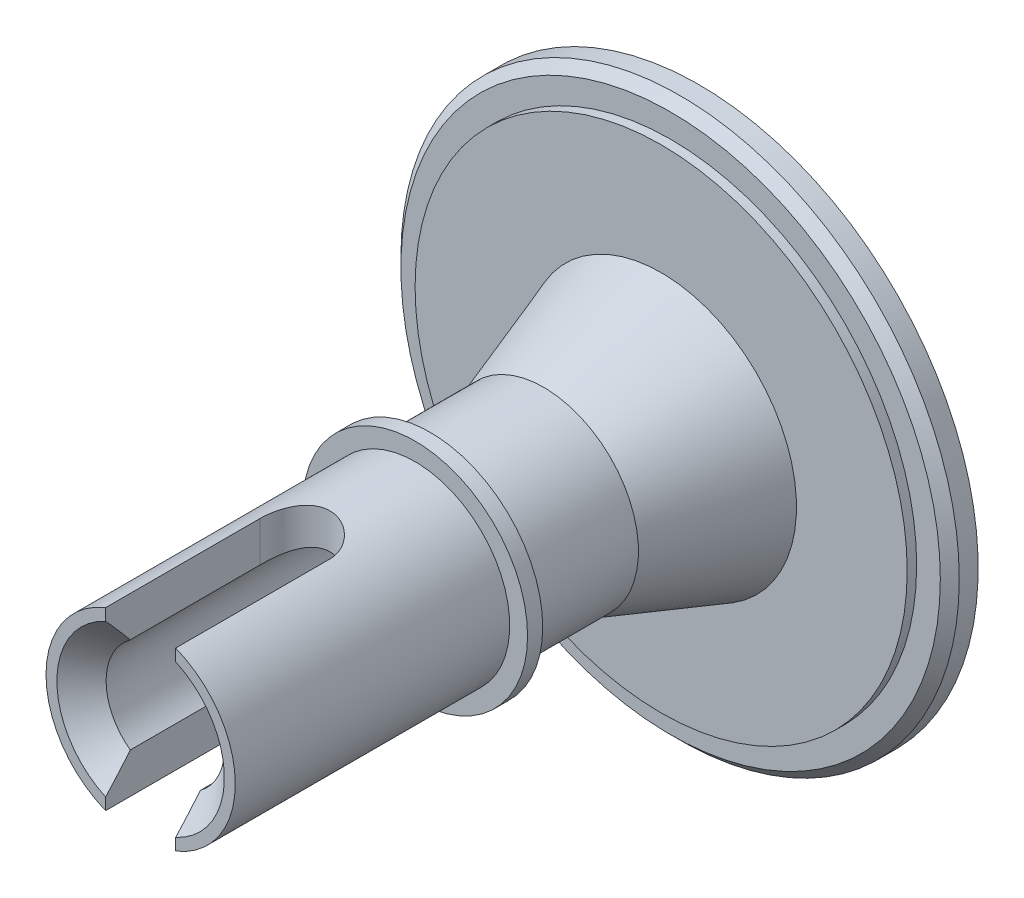
SolidWorks part; units mm, degrees
material "PVC hart"
ref_plane "Ebene vorne" through (0, 0, 0) normal (0, 0, 1) x (1, 0, 0)
ref_plane "Ebene oben" through (0, 0, 0) normal (0, 1, 0) x (1, 0, 0)
ref_plane "Ebene rechts" through (0, 0, 0) normal (1, 0, 0) x (0, 0, -1)
sketch "Skizze2" plane through (0, 0, 0) normal (1, 0, 0) x (0, 0, -1)
  line L0 (10.6064, 0) -> (-45.5592, 0) construction
  line L1 (0, 14.75) -> (-1.5, 14.75)
  line L2 (-1.5, 14.75) -> (-1.5, 13)
  line L3 (-1.5, 13) -> (-2, 13)
  line L4 (-2, 13) -> (-2, 7.15)
  line L5 (0.5, 7.5) -> (0, 7.5)
  line L6 (0.5, 7.5) -> (0.5, 9.5)
  line L7 (0.5, 9.5) -> (0, 9.5)
  line L8 (0, 9.5) -> (0, 12.65)
  line L9 (0, 7.5) -> (0, 3.9)
  line L10 (0, 3.9) -> (-2, 3.9)
  line L11 (-2, 3.9) -> (-2, 1.45)
  line L12 (-2, 1.45) -> (-4.5, 1.45)
  line L13 (-4.5, 1.45) -> (-4.5, 3.125)
  line L14 (-4.5, 3.125) -> (-29.5, 3.125)
  line L15 (-29.5, 3.125) -> (-29.5, 5)
  line L16 (-29.5, 5) -> (-15, 5)
  line L17 (0, 3.9) -> (0, 0) construction
  line L18 (0, 14.15) -> (-0.8, 14.15)
  line L19 (-0.8, 14.15) -> (-0.8, 12.65)
  line L20 (-0.8, 12.65) -> (0, 12.65)
  line L21 (0, 14.15) -> (0, 14.75)
  line L22 (-15, 5) -> (-15, 5.9425)
  line L23 (-15, 5.9425) -> (-14.2, 5.9425)
  line L24 (-14.2, 5.9425) -> (-14.2, 5)
  line L25 (-14.2, 5) -> (-8.2, 5)
  line L26 (-8.2, 5) -> (-2, 7.15)
  dimension "D1" = 29.5
  dimension "D2" = 26
  dimension "D3" = 2.5
  dimension "D4" = 1.5
  dimension "D5" = 2
  dimension "D6" = 30
  dimension "D7" = 10
  dimension "D8" = 2.5
  dimension "D9" = 25
  dimension "D10" = 19
  dimension "D11" = 15
  dimension "D12" = 2.9
  dimension "D13" = 7.8
  dimension "D14" = 6.25
  dimension "D15" = 25.3
  dimension "D16" = 1.5
  dimension "D17" = 0.7
  dimension "D18" = 11.8851
  dimension "D19" = 0.8
  dimension "D20" = 15.3
  dimension "D21" = 6
  dimension "D22" = 14.3
revolve "Rotation1" add sketch "Skizze2" angle 360 about L0
chamfer "Fase1" distance 0.5 angle 45 1 edges at (-14.75, 0, 1.5)
chamfer "Fase2" distance 1.3 angle 45 1 edges at (-3.125, 0, 29.5)
sketch "Skizze3" plane through (0, 0, 0) normal (0, 1, 0) x (1, 0, 0)
  line L0 (0, -21.35) -> (0, -29.5) construction
  line L1 (1.85, -21.35) -> (1.85, -29.5)
  line L2 (-1.85, -21.35) -> (-1.85, -29.5)
  line L3 (-5, -29.5) -> (5, -29.5) construction
  arc A0 (1.85, -21.35) -> (-1.85, -21.35) centre (0, -21.35) ccw
  arc A1 (-1.85, -29.5) -> (1.85, -29.5) centre (0, -29.5) ccw
  point P2 (0, -25.425)
  point P7 (0, -19.5)
  dimension "D1" = 10
  dimension "D2" = 3.7
extrude "Schnitt-Linear austragen1" cut sketch "Skizze3" against normal through all and the other way through all
sketch "Skizze4" plane through (0, 0, -0.5) normal (0, 0, -1) x (-1, 0, 0)
  line L0 (0, 8.5) -> (0, -8.5) construction
  line L1 (-10, 8.5) -> (10, 8.5)
  line L2 (-10, 8.5) -> (-10, -8.5)
  line L3 (-10, -8.5) -> (10, -8.5)
  line L4 (10, 8.5) -> (10, -8.5)
  dimension "D1" = 20
  dimension "D2" = 17
extrude "Schnitt-Linear austragen2" cut sketch "Skizze4" against normal up to surface (0.5 mm away) flip side to cut up to face at (-12.65, 0, 0)
